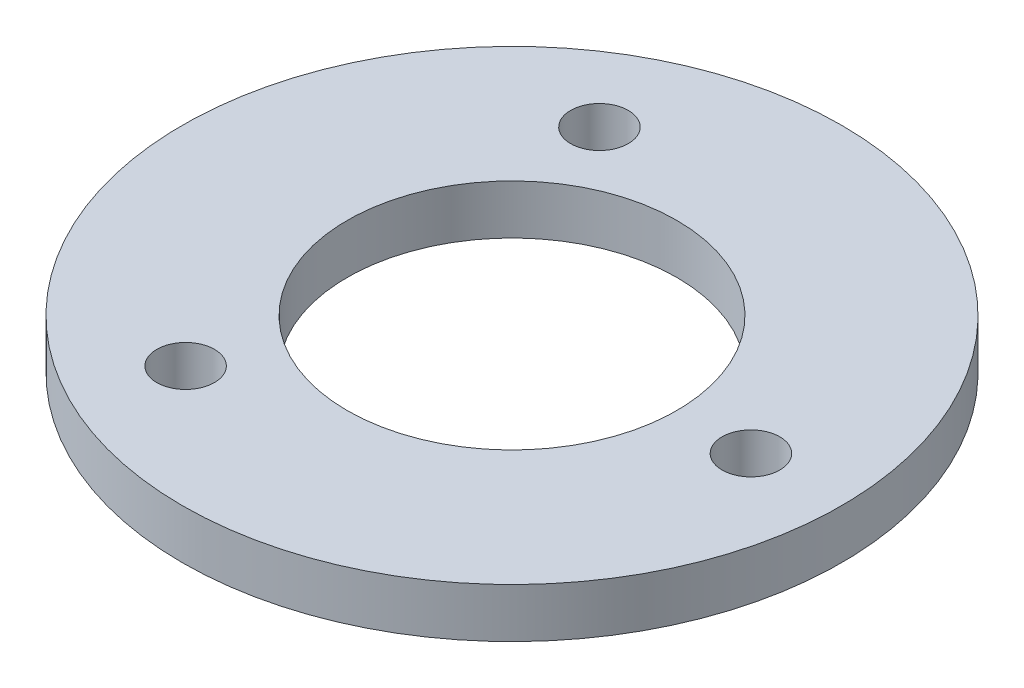
SolidWorks part; units mm, degrees
ref_plane "Płaszczyzna przednia" through (0, 0, 0) normal (0, 0, 1) x (1, 0, 0)
ref_plane "Płaszczyzna górna" through (0, 0, 0) normal (0, 1, 0) x (1, 0, 0)
ref_plane "Płaszczyzna prawa" through (0, 0, 0) normal (1, 0, 0) x (0, 0, -1)
sketch "Szkic1" plane through (0, 0, 0) normal (0, 1, 0) x (1, 0, 0)
  circle A0 centre (0, 0) radius 10
  circle A1 centre (0, 0) radius 20
  circle A2 centre (14.5, 0) radius 1.75
  circle A3 centre (-7.25, -12.5574) radius 1.75
  circle A4 centre (-7.25, 12.5574) radius 1.75
  point P13 (0, 0)
  dimension "D1" = 40
  dimension "D2" = 20
  dimension "D3" = 3.5
  dimension "D4" = 14.5
  dimension "D5" = 3
extrude "Dodanie-wyciągnięcie1" add sketch "Szkic1" along normal blind 3
